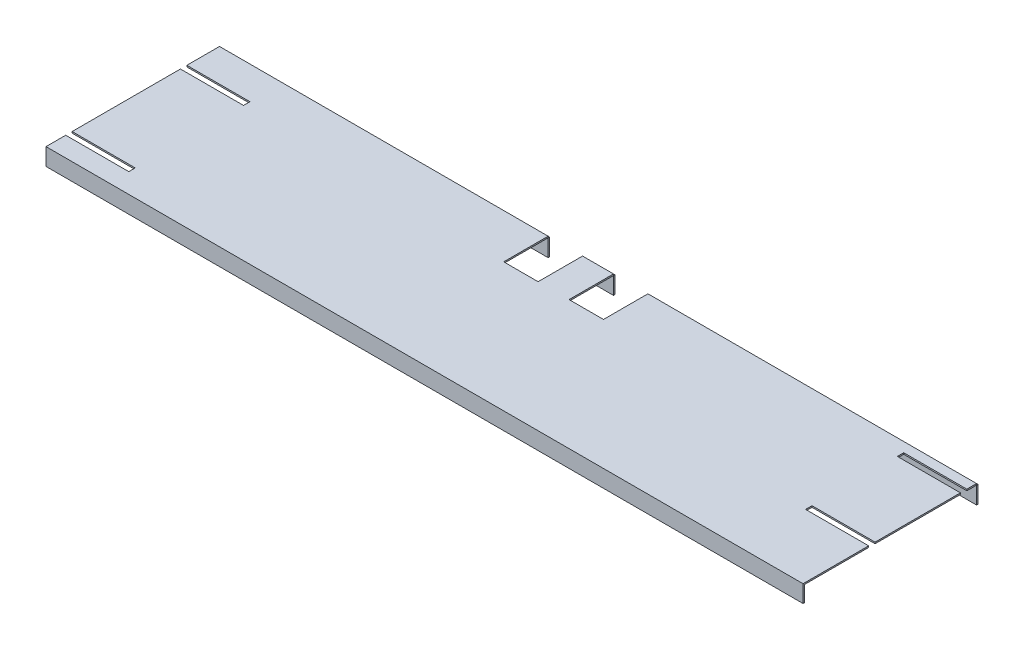
SolidWorks part; units mm, degrees
ref_plane "Front" through (0, 0, 0) normal (0, 0, 1) x (1, 0, 0)
ref_plane "Top" through (0, 0, 0) normal (0, 1, 0) x (1, 0, 0)
ref_plane "Right" through (0, 0, 0) normal (1, 0, 0) x (0, 0, -1)
sketch "Sketch1" plane through (0, 0, 0) normal (0, 1, 0) x (1, 0, 0)
  line L1 (0, 0) -> (838.2, 0)
  line L2 (0, 0) -> (0, -190.5)
  line L3 (0, -190.5) -> (838.2, -190.5)
  line L4 (838.2, 0) -> (838.2, -190.5)
  dimension "D1" = 838.2
  dimension "D2" = 190.5
extrude "Boss-Extrude1" add sketch "Sketch1" along normal blind 1.6002
sketch "Sketch3" plane through (0, 0, 190.5) normal (0, 0, 1) x (1, 0, 0)
  line L1 (0, 1.6002) -> (838.2, 1.6002)
  line L2 (0, 1.6002) -> (0, -17.4498)
  line L3 (0, -17.4498) -> (838.2, -17.4498)
  line L4 (838.2, 1.6002) -> (838.2, -17.4498)
  dimension "D1" = 19.05
extrude "Boss-Extrude2" add sketch "Sketch3" along normal blind 1.6002
sketch "Sketch4" plane through (0, 0, 0) normal (0, 0, -1) x (-1, 0, 0)
  line L1 (0, 0) -> (-838.2, 0)
  line L2 (0, 0) -> (0, -19.05)
  line L3 (0, -19.05) -> (-838.2, -19.05)
  line L4 (-838.2, 0) -> (-838.2, -19.05)
  dimension "D1" = 19.05
extrude "Boss-Extrude3" add sketch "Sketch4" along normal blind 1.6002
sketch "Sketch2" plane through (0, 1.6002, 0) normal (0, 1, 0) x (1, 0, 0)
  line L1 (363.855, -49.1998) -> (363.855, 1.6002)
  line L2 (363.855, 1.6002) -> (401.955, 1.6002)
  line L3 (363.855, -49.1998) -> (401.955, -49.1998)
  line L4 (401.955, 1.6002) -> (401.955, -49.1998)
  line L5 (436.245, -49.1998) -> (436.245, 1.6002)
  line L7 (436.245, 1.6002) -> (474.345, 1.6002)
  line L8 (474.345, 1.6002) -> (474.345, -49.1998)
  line L9 (419.1, 1.6002) -> (419.1, -67.7287) construction
  line L10 (436.245, -49.1998) -> (474.345, -49.1998)
  line L11 (401.955, -23.7998) -> (419.1, -23.7998) construction
  line L12 (436.245, -23.7998) -> (419.1, -23.7998) construction
  line L13 (838.2, 1.6002) -> (0, 1.6002) construction
  dimension "D1" = 50.8
  dimension "D2" = 50.8
  dimension "D3" = 38.1
  dimension "D4" = 38.1
  dimension "D5" = 34.29
extrude "Cut-Extrude1" cut sketch "Sketch2" against normal through all
sketch "Sketch6" plane through (0, 1.6002, 0) normal (0, 1, 0) x (1, 0, 0)
  line L0 (0, 0) -> (0, -192.1002) construction
  line L1 (0, -36.1442) -> (69.85, -36.1442)
  line L2 (0, -36.1442) -> (0, -43.2562)
  line L3 (0, -43.2562) -> (69.85, -43.2562)
  line L4 (69.85, -36.1442) -> (69.85, -43.2562)
  line L5 (838.2, -192.1002) -> (838.2, 0) construction
  line L6 (0, -163.1442) -> (69.85, -163.1442)
  line L7 (0, -163.1442) -> (0, -170.2562)
  line L8 (0, -170.2562) -> (69.85, -170.2562)
  line L9 (69.85, -163.1442) -> (69.85, -170.2562)
  line L10 (838.2, -10.7442) -> (768.35, -10.7442)
  line L11 (838.2, -10.7442) -> (838.2, -17.8562)
  line L14 (838.2, -17.8562) -> (768.35, -17.8562)
  line L15 (768.35, -10.7442) -> (768.35, -17.8562)
  line L16 (838.2, -192.1002) -> (0, -192.1002) construction
  line L17 (838.2, -112.3442) -> (768.35, -112.3442)
  line L18 (838.2, -112.3442) -> (838.2, -119.4562)
  line L19 (838.2, -119.4562) -> (768.35, -119.4562)
  line L20 (768.35, -112.3442) -> (768.35, -119.4562)
  dimension "D1" = 7.112
  dimension "D2" = 7.112
  dimension "D3" = 7.112
  dimension "D4" = 7.112
  dimension "D5" = 69.85
  dimension "D6" = 69.85
  dimension "D7" = 69.85
  dimension "D8" = 69.85
  dimension "D9" = 21.844
  dimension "D10" = 119.888
  dimension "D11" = 72.644
  dimension "D12" = 94.488
extrude "Cut-Extrude2" cut sketch "Sketch6" against normal through all
